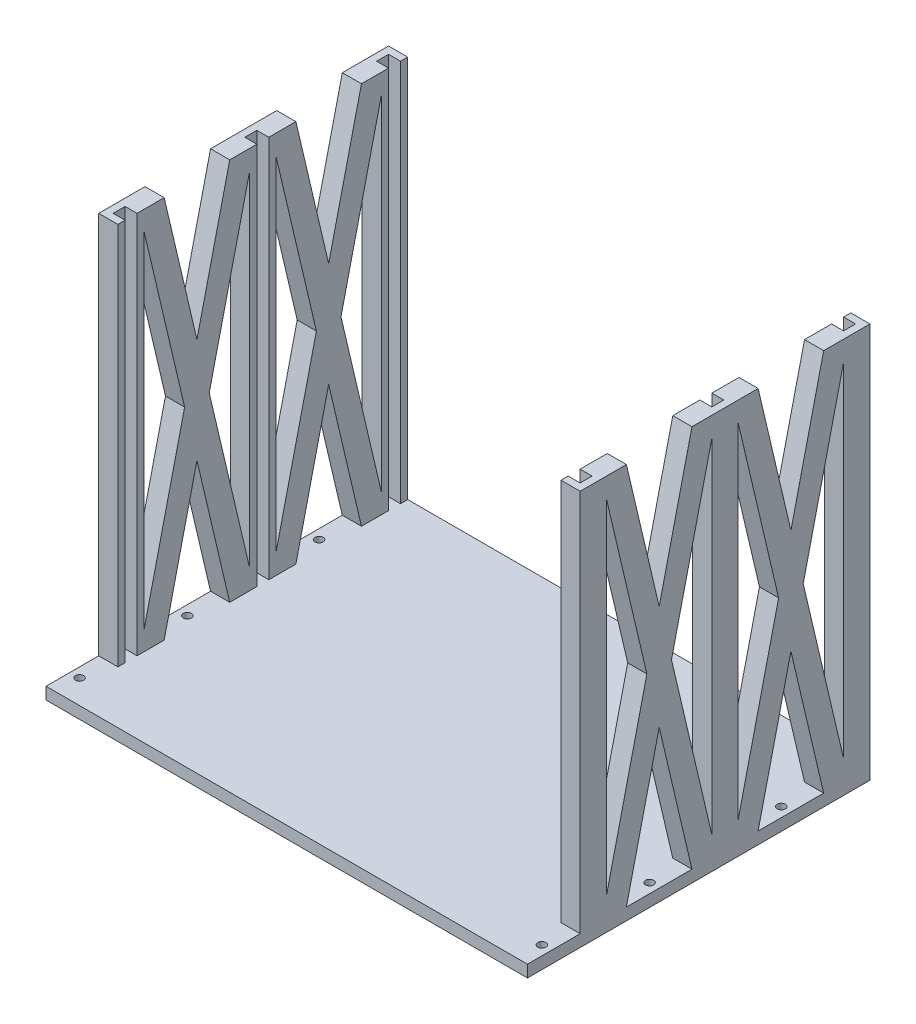
SolidWorks part; units mm, degrees
ref_plane "Front Plane" through (0, 0, 0) normal (0, 0, 1) x (1, 0, 0)
ref_plane "Top Plane" through (0, 0, 0) normal (0, 1, 0) x (1, 0, 0)
ref_plane "Right Plane" through (0, 0, 0) normal (1, 0, 0) x (0, 0, -1)
sketch "Sketch1" plane through (0, 0, 0) normal (0, 1, 0) x (1, 0, 0)
  line L0 (-100.5, 5.5) -> (-92.5, 5.5)
  line L1 (-97.5, -2.5) -> (97.5, -2.5) construction
  line L2 (-97.5, -2.5) -> (-97.5, 2.5) construction
  line L3 (-97.5, 2.5) -> (97.5, 2.5) construction
  line L4 (97.5, -2.5) -> (97.5, 2.5) construction
  line L5 (-97.5, -2.5) -> (97.5, 2.5) construction
  line L6 (-97.5, 2.5) -> (97.5, -2.5) construction
  line L7 (100.5, -5.5) -> (100.5, 5.5)
  line L8 (-100.5, -5.5) -> (-92.5, -5.5)
  line L9 (-100.5, -5.5) -> (-100.5, 5.5)
  line L10 (-92.5, 5.5) -> (-92.5, 2.5)
  line L11 (-92.5, 2.5) -> (-97.5, 2.5)
  line L12 (-97.5, 2.5) -> (-97.5, -2.5)
  line L13 (-97.5, -2.5) -> (-92.5, -2.5)
  line L14 (-92.5, -2.5) -> (-92.5, -5.5)
  line L15 (0, -55) -> (0, 55) construction
  line L16 (92.5, -2.5) -> (92.5, -5.5)
  line L17 (97.5, -2.5) -> (92.5, -2.5)
  line L18 (97.5, 2.5) -> (97.5, -2.5)
  line L19 (92.5, 2.5) -> (97.5, 2.5)
  line L20 (92.5, 5.5) -> (92.5, 2.5)
  line L21 (92.5, 5.5) -> (100.5, 5.5)
  line L22 (-100.5, 5.5) -> (100.5, 5.5) construction
  line L23 (92.5, -5.5) -> (100.5, -5.5)
  line L24 (-100.5, -5.5) -> (100.5, -5.5) construction
  point P0 (0, 0)
  dimension "D1" = 195
  dimension "D2" = 5
  dimension "D4" = 5
  dimension "D3" = 3
extrude "Boss-Extrude1" add sketch "Sketch1" along normal blind 160
pattern_linear "LPattern1" count 3 spacing 55 along (0, 0, 1) of "Boss-Extrude1"
sketch "Sketch2" plane through (0, 0, 0) normal (0, -1, 0) x (1, 0, 0)
  line L1 (-100.5, -5.5) -> (100.5, -5.5)
  line L2 (-100.5, -5.5) -> (-100.5, 137.5)
  line L3 (-100.5, 137.5) -> (100.5, 137.5)
  line L4 (100.5, -5.5) -> (100.5, 137.5)
  line L5 (-97.5, 107.5) -> (-92.5, 107.5) construction
  point P5 (100.5, -5.5)
  dimension "D1" = 30
extrude "Boss-Extrude2" add sketch "Sketch2" along normal blind 5
sketch "Sketch3" plane through (-100.5, 0, 0) normal (-1, 0, 0) x (0, 0, 1)
  line L0 (5.5, 160) -> (13.8165, 160)
  line L1 (13.8165, 160) -> (27.5, 101.8342)
  line L2 (27.5, 101.8342) -> (41.1835, 160)
  line L3 (41.1835, 160) -> (49.5, 160)
  line L5 (49.5, 0) -> (41.1835, 0)
  line L6 (49.5, 0) -> (5.5, 0) construction
  line L7 (41.1835, 0) -> (27.5, 58.1658)
  line L8 (27.5, 58.1658) -> (13.8165, 0)
  line L9 (13.8165, 0) -> (5.5, 0)
  line L11 (5.5, 160) -> (5.5, 151.6835)
  line L12 (5.5, 160) -> (5.5, 0) construction
  line L13 (5.5, 151.6835) -> (22.3635, 80)
  line L14 (22.3635, 80) -> (5.5, 8.3165)
  line L15 (5.5, 8.3165) -> (5.5, 0)
  line L16 (49.5, 0) -> (49.5, 8.3165)
  line L17 (49.5, 160) -> (49.5, 0) construction
  line L18 (49.5, 8.3165) -> (32.6365, 80)
  line L19 (32.6365, 80) -> (49.5, 151.6835)
  line L20 (49.5, 151.6835) -> (49.5, 160)
  line L21 (104.5, 151.6835) -> (104.5, 160)
  line L22 (96.1835, 160) -> (104.5, 160)
  line L23 (82.5, 101.8342) -> (96.1835, 160)
  line L24 (68.8165, 160) -> (82.5, 101.8342)
  line L25 (60.5, 160) -> (68.8165, 160)
  line L26 (60.5, 160) -> (60.5, 151.6835)
  line L27 (60.5, 151.6835) -> (77.3635, 80)
  line L28 (77.3635, 80) -> (60.5, 8.3165)
  line L29 (60.5, 8.3165) -> (60.5, 0)
  line L30 (68.8165, 0) -> (60.5, 0)
  line L31 (82.5, 58.1658) -> (68.8165, 0)
  line L32 (96.1835, 0) -> (82.5, 58.1658)
  line L33 (104.5, 0) -> (96.1835, 0)
  line L34 (104.5, 0) -> (104.5, 8.3165)
  line L35 (104.5, 8.3165) -> (87.6365, 80)
  line L36 (87.6365, 80) -> (104.5, 151.6835)
  point P28 (265.9826, 160)
  point P43 (0, 0)
  point P44 (65.5, 160)
  dimension "D1" = 10
  dimension "D2" = 2
extrude "Boss-Extrude3" add sketch "Sketch3" against normal blind 8
mirror "Mirror1" about plane through (0, 0, 0) normal (1, 0, 0) of "Boss-Extrude3"
hole_wizard "M3 Clearance Hole1" positions "Sketch4" profile "Sketch5" hole size "M3" standard "ANSI Metric"
sketch "Sketch4" plane through (0, 0, 0) normal (0, 1, 0) x (1, 0, 0)
  line L0 (-92.5, -27.5) -> (-100.5, -27.5) construction
  line L1 (-92.5, -82.5) -> (-100.5, -82.5) construction
  line L2 (92.5, -82.5) -> (100.5, -82.5) construction
  line L3 (92.5, -27.5) -> (100.5, -27.5) construction
  line L4 (-96.5, -27.5) -> (-96.5, -82.5) construction
  line L5 (-96.5, -82.5) -> (-96.5, -127.5) construction
  point P0 (-96.5, -27.5)
  point P4 (-96.5, -82.5)
  point P8 (96.5, -82.5)
  point P12 (96.5, -27.5)
  point P16 (-96.5, -127.5)
  point P18 (96.5, -127.5)
  point P27 (0, 0)
  point P28 (0, 0)
  dimension "D1" = 45
sketch "Sketch5" plane through (-96.5, 0, 27.5) normal (1, 0, 0) x (0, 0, 1)
  line L0 (0, 0) -> (0, 5)
  line L1 (0, 5) -> (1.7, 5)
  line L2 (1.7, 5) -> (1.7, 0)
  line L5 (1.7, 0) -> (0, 0)
  line L11 (0, -6.35) -> (0, 107.95) construction
  dimension "Thru Hole Dia." = 3.4
  dimension "Thru Hole Depth" = 5
